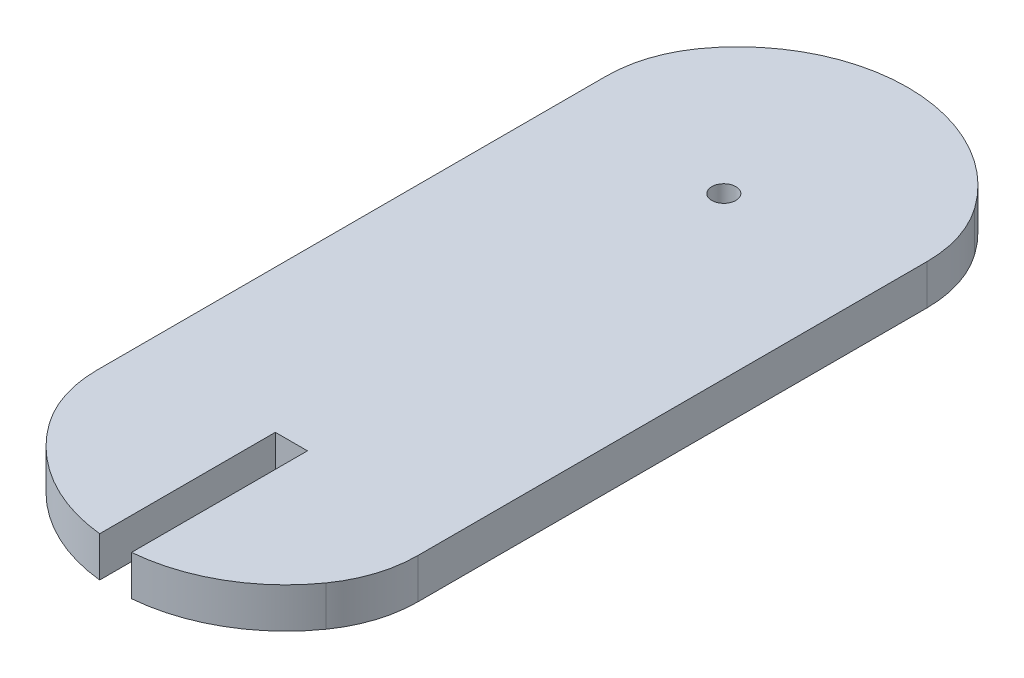
SolidWorks part; units mm, degrees
ref_plane "Front Plane" through (0, 0, 0) normal (0, 0, 1) x (1, 0, 0)
ref_plane "Top Plane" through (0, 0, 0) normal (0, 1, 0) x (1, 0, 0)
ref_plane "Right Plane" through (0, 0, 0) normal (1, 0, 0) x (0, 0, -1)
sketch "Sketch2" plane through (0, 0, 0) normal (0, 1, 0) x (1, 0, 0)
  line L1 (-20, -35) -> (20, -35)
  line L2 (-20, -35) -> (-20, 35)
  line L3 (-20, 35) -> (20, 35)
  line L4 (20, -35) -> (20, 35)
  line L5 (-20, -35) -> (20, 35) construction
  line L6 (-20, 35) -> (20, -35) construction
  arc A0 (-20, 35) -> (20, 35) centre (0, 28.172) cw
  arc A1 (-20, -35) -> (20, -35) centre (0, -28.1826) ccw
  point P0 (0, 0)
  dimension "D3" = 21.1334
  dimension "D4" = 21.13
  dimension "D1" = 40
  dimension "D2" = 70
extrude "Boss-Extrude1" add sketch "Sketch2" along normal blind 5 contours L1 A1 | L1 L4 L3 L2 | A0 L3
fillet "Fillet1" radius 15 4 edges at (20, 2.5, 35) (-20, 2.5, 35) (-20, 2.5, -35) (20, 2.5, -35)
sketch "Sketch3" plane through (0, 0, 0) normal (0, -1, 0) x (1, 0, 0)
  line L0 (0, -49.3055) -> (0, 49.3126) construction
  line L1 (0, 49.3126) -> (1.8237, 49.3126)
  line L2 (1.8237, 49.3126) -> (1.8237, 27.3126)
  line L3 (1.8237, 27.3126) -> (-2.1763, 27.3126)
  line L4 (-2.1763, 27.3126) -> (-2.1763, 49.3126)
  line L5 (-2.1763, 49.3126) -> (0, 49.3126)
  line L6 (20, 31.729) -> (20, -31.7243) construction
  arc A0 (-17.2281, -40.4119) -> (17.2281, -40.4119) centre (0, -28.172) ccw construction
  arc A1 (17.2349, 40.407) -> (-17.2349, 40.407) centre (0, 28.1826) ccw construction
  dimension "D1" = 4
  dimension "D2" = 22
  dimension "D3" = 18.1763
extrude "Cut-Extrude1" cut sketch "Sketch3" against normal through all
sketch "Sketch4" plane through (0, 0, 0) normal (0, -1, 0) x (1, 0, 0)
  line L1 (20, 31.729) -> (20, -31.7243) construction
  circle A0 centre (0, -26.3874) radius 1.5
  arc A1 (-17.2281, -40.4119) -> (17.2281, -40.4119) centre (0, -28.172) ccw construction
  point P7 (0, -49.3055)
  dimension "D1" = 3
  dimension "D2" = 22.9181
  dimension "D3" = 20
extrude "Cut-Extrude2" cut sketch "Sketch4" against normal through all
